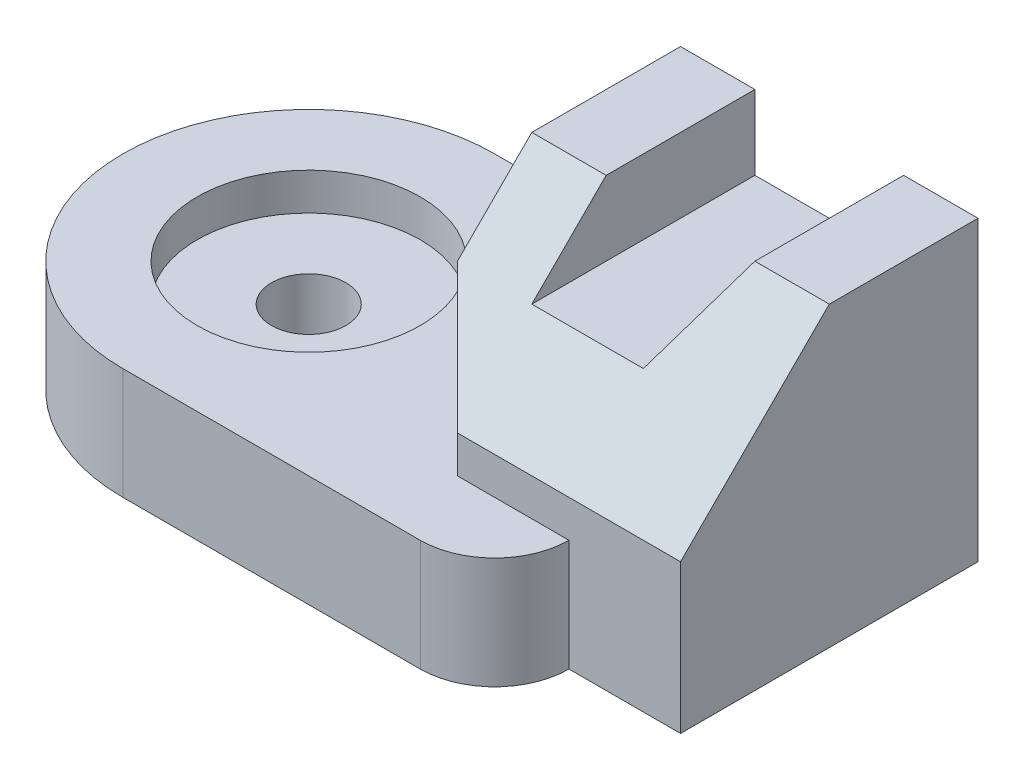
SolidWorks part; units mm, degrees
ref_plane "Front" through (0, 0, 0) normal (0, 0, 1) x (1, 0, 0)
ref_plane "Top" through (0, 0, 0) normal (0, 1, 0) x (1, 0, 0)
ref_plane "Right" through (0, 0, 0) normal (1, 0, 0) x (0, 0, -1)
sketch "Sketch1" plane through (0, 0, 0) normal (0, 1, 0) x (1, 0, 0)
  line L0 (0, 5) -> (13, 5)
  line L1 (13, 5) -> (13, -3)
  line L2 (13, -3) -> (10, -3)
  line L3 (8, -5) -> (0, -5)
  circle A0 centre (0, 0) radius 1
  arc A1 (0, 5) -> (0, -5) centre (0, 0) ccw
  arc A2 (10, -3) -> (8, -5) centre (8, -3) cw
  dimension "D1" = 2
  dimension "D2" = 5
  dimension "D6" = 2
  dimension "D3" = 5
  dimension "D4" = 8
  dimension "D5" = 3
  dimension "D7" = 13
  dimension "D8" = 8
extrude "Boss-Extrude1" add sketch "Sketch1" along normal blind 3
sketch "Sketch2" plane through (0, 3, 0) normal (0, 1, 0) x (1, 0, 0)
  circle A0 centre (0, 0) radius 3
  dimension "D1" = 6
extrude "Cut-Extrude1" cut sketch "Sketch2" against normal blind 1
sketch "Sketch3" plane through (0, 3, 0) normal (0, 1, 0) x (1, 0, 0)
  line L0 (13, 5) -> (0, 5) construction
  line L1 (13, -3) -> (7, -3)
  line L2 (13, -3) -> (13, 5)
  line L3 (13, 5) -> (5, 5)
  line L4 (5, -1) -> (5, 5)
  line L5 (7, -3) -> (5, -1)
  point P3 (5, -3)
  dimension "D1" = 8
extrude "Boss-Extrude2" add sketch "Sketch3" along normal blind 5
sketch "Sketch4" plane through (13, 0, 0) normal (1, 0, 0) x (0, 0, -1)
  line L0 (-3, 4) -> (1, 8)
  line L1 (-3, 8) -> (-3, 0) construction
  line L2 (-3, 8) -> (5, 8) construction
  line L3 (1, 8) -> (-3, 8)
  line L4 (-3, 8) -> (-3, 4)
  dimension "D1" = 1
  dimension "D2" = 4
extrude "Cut-Extrude2" cut sketch "Sketch4" against normal blind 13
sketch "Sketch5" plane through (0, 0, -5) normal (0, 0, -1) x (-1, 0, 0)
  line L0 (-7, 8) -> (-7, 6)
  line L1 (-13, 8) -> (-5, 8) construction
  line L2 (-7, 6) -> (-10, 6)
  line L3 (-10, 6) -> (-11, 8)
  line L4 (-11, 8) -> (-7, 8)
  line L5 (-5, 6) -> (-5, 8) construction
  dimension "D1" = 2
  dimension "D2" = 2
  dimension "D3" = 4
  dimension "D4" = 3
extrude "Cut-Extrude3" cut sketch "Sketch5" against normal blind 13
